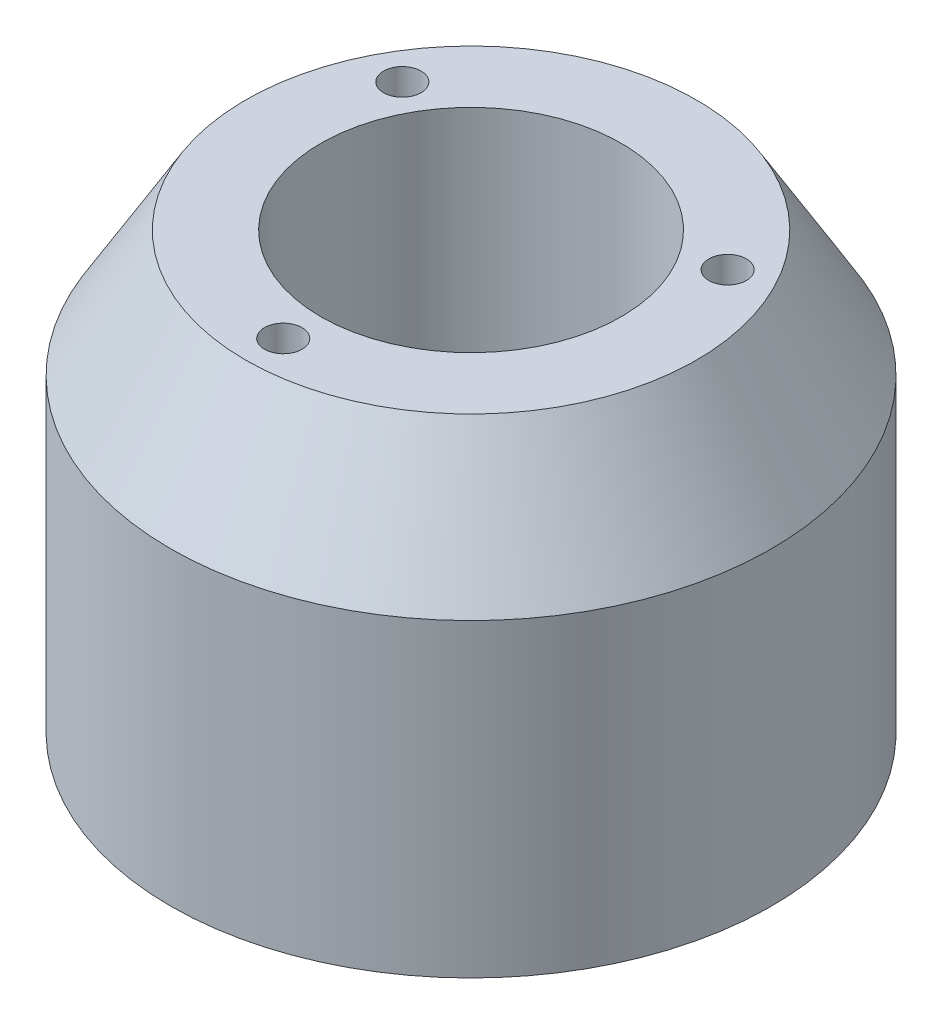
SolidWorks part; units mm, degrees
ref_plane "Plan de face" through (0, 0, 0) normal (0, 0, 1) x (1, 0, 0)
ref_plane "Plan de dessus" through (0, 0, 0) normal (0, 1, 0) x (1, 0, 0)
ref_plane "Plan de droite" through (0, 0, 0) normal (1, 0, 0) x (0, 0, -1)
sketch "Esquisse1" plane through (0, 0, 0) normal (0, 0, 1) x (1, 0, 0)
  line L0 (0, 0) -> (40, 0)
  line L1 (40, 0) -> (40, 41.2)
  line L2 (40, 41.2) -> (30, 57.9407)
  line L3 (30, 57.9407) -> (0, 57.9407)
  line L4 (0, 57.9407) -> (0, 0)
  dimension "D1" = 40
  dimension "D2" = 41.2
  dimension "D3" = 19.5
  dimension "D4" = 30
  dimension "D5" = 57.9407
revolve "Révolution1" add sketch "Esquisse1" angle 360 about L4
sketch "Esquisse2" plane through (0, 57.9407, 0) normal (0, 1, 0) x (1, 0, 0)
  circle A0 centre (0, 0) radius 20
  dimension "D1" = 40
extrude "Enlèv. mat.-Extru.1" cut sketch "Esquisse2" against normal through all
sketch "Esquisse3" plane through (0, 0, 0) normal (0, -1, 0) x (-1, 0, 0)
  line L0 (0, 44.5296) -> (0, -44.5021) construction
  line L1 (52.9775, 0) -> (-48.3964, 0) construction
  circle A0 centre (30, 0) radius 3
  circle A1 centre (0, -30) radius 3
  circle A3 centre (0, 0) radius 40 construction
  circle A4 centre (0, 0) radius 20 construction
  circle A5 centre (-30, 0) radius 3
  circle A6 centre (0, 30) radius 3
  dimension "D1" = 6
  dimension "D2" = 6
  dimension "D3" = 30
  dimension "D4" = 30
sketch "Esquisse4" plane through (0, 57.9407, 0) normal (0, 1, 0) x (1, 0, 0)
  line L0 (0, -45.1516) -> (0, 47.7125) construction
  line L1 (0, 0) -> (50.1522, -28.9554) construction
  circle A0 centre (0, -25) radius 3
  circle A1 centre (0, 0) radius 20 construction
  circle A2 centre (21.6506, 12.5) radius 3
  circle A3 centre (-21.6506, 12.5) radius 3
  dimension "D1" = 6
  dimension "D2" = 25
  dimension "D3" = 60
hole_wizard "Trou taraudé M61" positions "Esquisse3D1" profile "Esquisse6" tap size "M6" standard "ISO"
sketch3d "Esquisse3D1"
  point P0 (-21.6506, 57.9407, -12.5)
  point P3 (21.6506, 57.9407, -12.5)
  point P6 (0, 57.9407, 25)
sketch "Esquisse6" plane through (-21.6506, 57.9407, -12.5) normal (1, 0, 0) x (0, 0, 1)
  line L0 (0, 0) -> (0, 18.5022)
  line L1 (0, 18.5022) -> (2.5, 17)
  line L2 (2.5, 17) -> (2.5, 0)
  line L5 (2.5, 0) -> (0, 0)
  line L10 (0, 18.5022) -> (-2.5, 17) construction
  line L11 (0, -6.35) -> (0, 107.95) construction
  dimension "Diamètre du trou pour taraudage" = 5
  dimension "Profondeur du trou pour taraudage" = 17
  dimension "Angle de pointe" = 118
cosmetic thread "Filetage de perçage8" parameters "D1"=15, "D2"=6
cosmetic thread "Filetage de perçage9" parameters "D1"=15, "D2"=6
cosmetic thread "Filetage de perçage10" parameters "D1"=15, "D2"=6
hole_wizard "Trou taraudé M62" positions "Esquisse3D2" profile "Esquisse7" tap size "M6" standard "ISO"
sketch3d "Esquisse3D2"
  point P0 (0, 0, 30)
  point P3 (30, 0, 0)
  point P6 (0, 0, -30)
  point P9 (-30, 0, 0)
sketch "Esquisse7" plane through (0, 0, 30) normal (1, 0, 0) x (0, 0, -1)
  line L0 (0, 0) -> (0, 29.5022)
  line L1 (0, 29.5022) -> (2.5, 28)
  line L2 (2.5, 28) -> (2.5, 0)
  line L5 (2.5, 0) -> (0, 0)
  line L10 (0, 29.5022) -> (-2.5, 28) construction
  line L11 (0, -6.35) -> (0, 107.95) construction
  dimension "Diamètre du trou pour taraudage" = 5
  dimension "Profondeur du trou pour taraudage" = 28
  dimension "Angle de pointe" = 118
cosmetic thread "Filetage de perçage4" parameters "D1"=25, "D2"=6
cosmetic thread "Filetage de perçage5" parameters "D1"=25, "D2"=6
cosmetic thread "Filetage de perçage6" parameters "D1"=25, "D2"=6
cosmetic thread "Filetage de perçage7" parameters "D1"=25, "D2"=6
